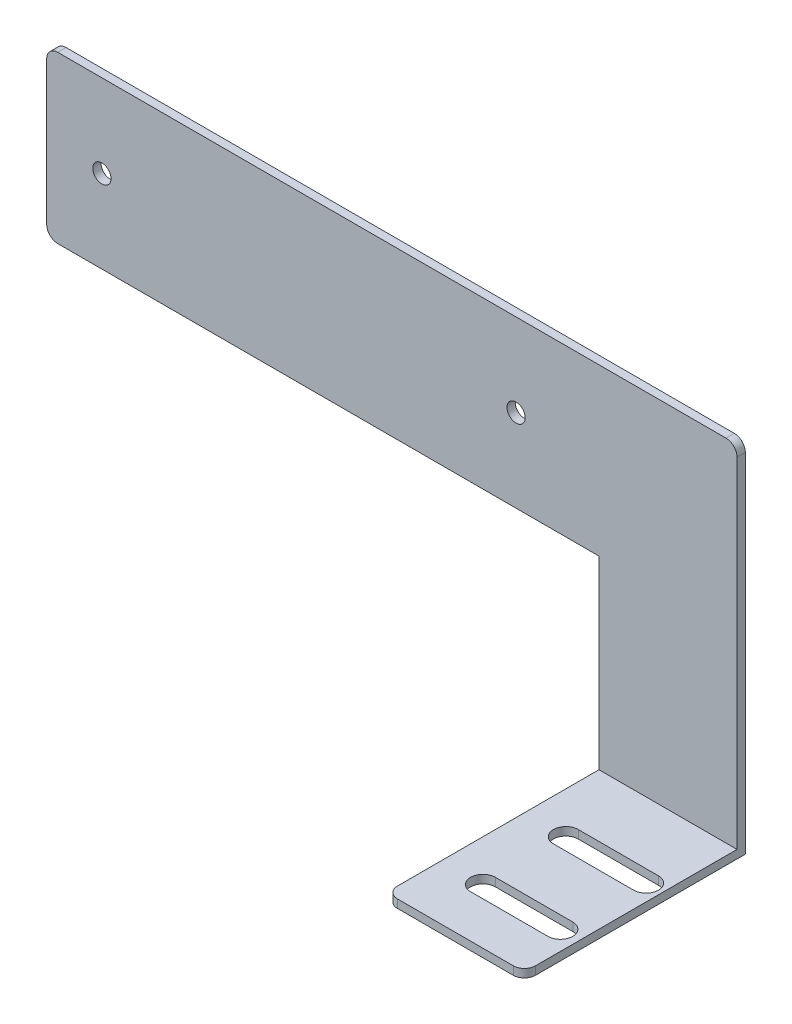
SolidWorks part; units mm, degrees
ref_plane "Front Plane" through (0, 0, 0) normal (0, 0, 1) x (1, 0, 0)
ref_plane "Top Plane" through (0, 0, 0) normal (0, 1, 0) x (1, 0, 0)
ref_plane "Right Plane" through (0, 0, 0) normal (1, 0, 0) x (0, 0, -1)
sketch "Sketch1" plane through (0, 0, 0) normal (0, 0, 1) x (1, 0, 0)
  line L0 (-54.0906, -2.8301) -> (70.9094, -2.8301)
  line L1 (70.9094, -2.8301) -> (70.9094, -67.8301)
  line L2 (70.9094, -67.8301) -> (45.9094, -67.8301)
  line L3 (45.9094, -67.8301) -> (45.9094, -32.8301)
  line L4 (45.9094, -32.8301) -> (-54.0906, -32.8301)
  line L5 (-54.0906, -32.8301) -> (-54.0906, -2.8301)
  dimension "D1" = 125
  dimension "D2" = 30
  dimension "D3" = 65
  dimension "D4" = 100
extrude "Boss-Extrude1" add sketch "Sketch1" along normal blind 1.5
sketch "Sketch2" plane through (0, 0, 1.5) normal (0, 0, 1) x (1, 0, 0)
  line L0 (70.9094, -67.8301) -> (70.9094, -2.8301) construction
  line L1 (45.9094, -67.8301) -> (70.9094, -67.8301)
  line L2 (45.9094, -67.8301) -> (45.9094, -66.3301)
  line L3 (45.9094, -66.3301) -> (70.9094, -66.3301)
  line L4 (70.9094, -67.8301) -> (70.9094, -66.3301)
  dimension "D1" = 1.5
extrude "Boss-Extrude2" add sketch "Sketch2" along normal blind 38.5
fillet "Fillet1" radius 2 5 edges at (70.9094, -2.8301, 0.75) (70.9094, -67.0801, 40) (45.9094, -67.0801, 40) (-54.0906, -32.8301, 0.75) (-54.0906, -2.8301, 0.75)
sketch "Sketch3" plane through (0, -67.8301, 0) normal (0, -1, 0) x (1, 0, 0)
  line L1 (53.4094, 32.25) -> (67.4173, 32.25)
  line L3 (53.4094, 27.75) -> (67.4173, 27.75)
  line L5 (67.9364, 12.75) -> (53.4094, 12.75)
  line L7 (67.9364, 17.25) -> (53.4094, 17.25)
  arc A0 (53.4094, 32.25) -> (53.4094, 27.75) centre (53.4094, 30) ccw
  arc A1 (67.4173, 27.75) -> (67.4173, 32.25) centre (67.4173, 30) ccw
  arc A2 (67.9364, 12.75) -> (67.9364, 17.25) centre (67.9364, 15) ccw
  arc A3 (53.4094, 17.25) -> (53.4094, 12.75) centre (53.4094, 15) ccw
  dimension "D1" = 4.5
extrude "Cut-Extrude1" cut sketch "Sketch3" against normal blind 38.5
hole_wizard "M4x0.7 Tapped Hole1" positions "Sketch4" profile "Sketch5" tap size "M4x0.7" standard "ANSI Metric" end condition through all
sketch "Sketch4" plane through (0, 0, 1.5) normal (0, 0, 1) x (1, 0, 0)
  line L0 (-54.0906, -4.8301) -> (-54.0906, -30.8301) construction
  line L1 (68.9094, -2.8301) -> (-52.0906, -2.8301) construction
  point P0 (-44.0906, -17.8301)
  point P2 (30.9094, -17.8301)
  dimension "D1" = 75
  dimension "D2" = 10
  dimension "D3" = 15
  dimension "D4" = 15
sketch "Sketch5" plane through (-44.0906, -17.8301, 1.5) normal (1, 0, 0) x (0, -1, 0)
  line L0 (0, 0) -> (0, 1.5)
  line L1 (0, 1.5) -> (1.65, 1.5)
  line L2 (1.65, 1.5) -> (1.65, 0)
  line L5 (1.65, 0) -> (0, 0)
  line L11 (0, -6.35) -> (0, 107.95) construction
  dimension "Thru Tap Drill Dia." = 3.3
  dimension "Thru Tap Drill Depth" = 1.5
cosmetic thread "Hole Thread1" parameters "D2"=4
cosmetic thread "Hole Thread2" parameters "D2"=4
